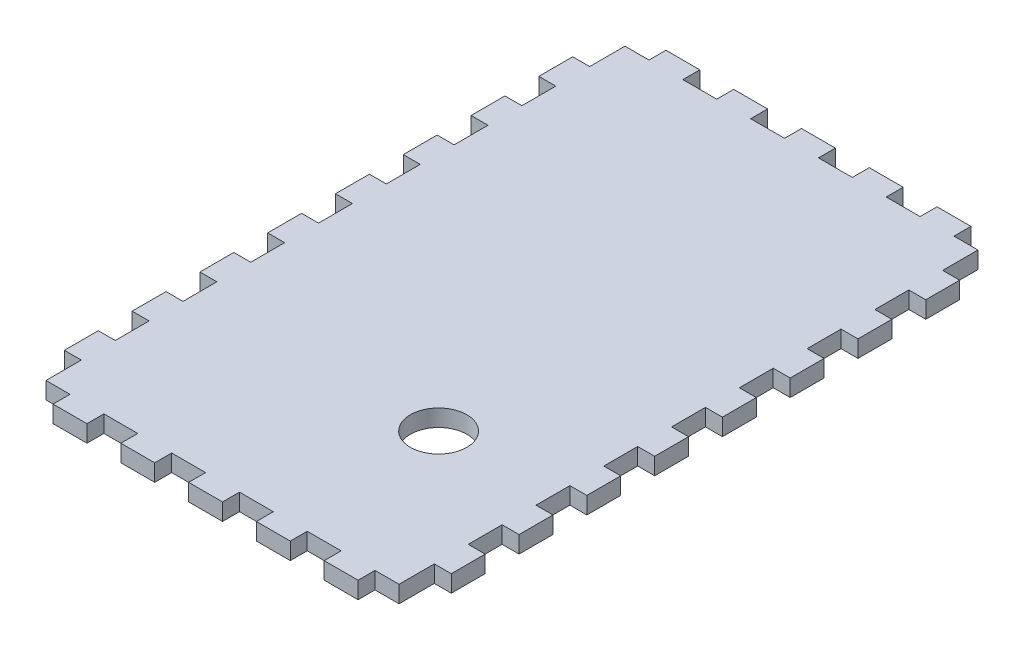
SolidWorks part; units mm, degrees
ref_plane "Front Plane" through (0, 0, 0) normal (0, 0, 1) x (1, 0, 0)
ref_plane "Top Plane" through (0, 0, 0) normal (0, 1, 0) x (1, 0, 0)
ref_plane "Right Plane" through (0, 0, 0) normal (1, 0, 0) x (0, 0, -1)
sketch "Sketch3" plane through (0, 0, 0) normal (0, 1, 0) x (1, 0, 0)
  line L231 (-62.5, -102.5) -> (62.5, -102.5)
  line L232 (-62.5, -102.5) -> (-62.5, 102.5)
  line L233 (-62.5, 102.5) -> (62.5, 102.5)
  line L234 (62.5, -102.5) -> (62.5, 102.5)
  line L235 (-62.5, -102.5) -> (62.5, 102.5) construction
  line L236 (-62.5, 102.5) -> (62.5, -102.5) construction
  point P66 (0, 0)
  dimension "D3" = 205
  dimension "D4" = 125
extrude "Boss-Extrude1" add sketch "Sketch3" along normal blind 6
sketch "Sketch5" plane through (0, 6, 0) normal (0, 1, 0) x (1, 0, 0)
  line L0 (62.5, 102.5) -> (-62.5, 102.5) construction
  line L1 (-54, 102.5) -> (-42, 102.5)
  line L2 (-54, 102.5) -> (-54, 108.5)
  line L3 (-54, 108.5) -> (-42, 108.5)
  line L4 (-42, 102.5) -> (-42, 108.5)
  line L5 (-30, 102.5) -> (-30, 108.5)
  line L6 (-30, 102.5) -> (-18, 102.5)
  line L7 (-18, 102.5) -> (-18, 108.5)
  line L8 (-30, 108.5) -> (-18, 108.5)
  line L9 (-6, 102.5) -> (-6, 108.5)
  line L10 (-6, 102.5) -> (6, 102.5)
  line L11 (6, 102.5) -> (6, 108.5)
  line L12 (-6, 108.5) -> (6, 108.5)
  line L13 (18, 102.5) -> (18, 108.5)
  line L14 (18, 102.5) -> (30, 102.5)
  line L15 (30, 102.5) -> (30, 108.5)
  line L16 (18, 108.5) -> (30, 108.5)
  line L17 (42, 102.5) -> (42, 108.5)
  line L18 (42, 102.5) -> (54, 102.5)
  line L19 (54, 102.5) -> (54, 108.5)
  line L20 (42, 108.5) -> (54, 108.5)
  line L41 (-62.5, 102.5) -> (-62.5, -102.5) construction
  line L43 (62.5, -102.5) -> (62.5, 102.5) construction
  line L44 (-62.5, 90) -> (-68.5, 90)
  line L45 (-62.5, 90) -> (-62.5, 78)
  line L46 (-62.5, 78) -> (-68.5, 78)
  line L47 (-68.5, 90) -> (-68.5, 78)
  line L48 (68.5, 90) -> (68.5, 78)
  line L49 (68.5, 90) -> (62.5, 90)
  line L50 (62.5, 90) -> (62.5, 78)
  line L51 (68.5, 78) -> (62.5, 78)
  line L52 (68.5, 66) -> (68.5, 54)
  line L53 (68.5, 66) -> (62.5, 66)
  line L54 (62.5, 66) -> (62.5, 54)
  line L55 (68.5, 54) -> (62.5, 54)
  line L56 (68.5, 42) -> (68.5, 30)
  line L57 (68.5, 42) -> (62.5, 42)
  line L58 (62.5, 42) -> (62.5, 30)
  line L59 (68.5, 30) -> (62.5, 30)
  line L60 (68.5, 18) -> (68.5, 6)
  line L61 (68.5, 18) -> (62.5, 18)
  line L62 (62.5, 18) -> (62.5, 6)
  line L63 (68.5, 6) -> (62.5, 6)
  line L64 (68.5, -6) -> (68.5, -18)
  line L65 (68.5, -6) -> (62.5, -6)
  line L66 (62.5, -6) -> (62.5, -18)
  line L67 (68.5, -18) -> (62.5, -18)
  line L68 (68.5, -30) -> (68.5, -42)
  line L69 (68.5, -30) -> (62.5, -30)
  line L70 (62.5, -30) -> (62.5, -42)
  line L71 (68.5, -42) -> (62.5, -42)
  line L72 (68.5, -54) -> (68.5, -66)
  line L73 (68.5, -54) -> (62.5, -54)
  line L74 (62.5, -54) -> (62.5, -66)
  line L75 (68.5, -66) -> (62.5, -66)
  line L76 (68.5, -78) -> (68.5, -90)
  line L77 (68.5, -78) -> (62.5, -78)
  line L78 (62.5, -78) -> (62.5, -90)
  line L79 (68.5, -90) -> (62.5, -90)
  line L80 (-62.5, 66) -> (-62.5, 54)
  line L81 (-62.5, 66) -> (-68.5, 66)
  line L82 (-68.5, 66) -> (-68.5, 54)
  line L83 (-62.5, 54) -> (-68.5, 54)
  line L84 (-62.5, 42) -> (-62.5, 30)
  line L85 (-62.5, 42) -> (-68.5, 42)
  line L86 (-68.5, 42) -> (-68.5, 30)
  line L87 (-62.5, 30) -> (-68.5, 30)
  line L88 (-62.5, 18) -> (-62.5, 6)
  line L89 (-62.5, 18) -> (-68.5, 18)
  line L90 (-68.5, 18) -> (-68.5, 6)
  line L91 (-62.5, 6) -> (-68.5, 6)
  line L92 (-62.5, -6) -> (-62.5, -18)
  line L93 (-62.5, -6) -> (-68.5, -6)
  line L94 (-68.5, -6) -> (-68.5, -18)
  line L95 (-62.5, -18) -> (-68.5, -18)
  line L96 (-62.5, -30) -> (-62.5, -42)
  line L97 (-62.5, -30) -> (-68.5, -30)
  line L98 (-68.5, -30) -> (-68.5, -42)
  line L99 (-62.5, -42) -> (-68.5, -42)
  line L100 (-62.5, -54) -> (-62.5, -66)
  line L101 (-62.5, -54) -> (-68.5, -54)
  line L102 (-68.5, -54) -> (-68.5, -66)
  line L103 (-62.5, -66) -> (-68.5, -66)
  line L104 (-62.5, -78) -> (-62.5, -90)
  line L105 (-62.5, -78) -> (-68.5, -78)
  line L106 (-68.5, -78) -> (-68.5, -90)
  line L107 (-62.5, -90) -> (-68.5, -90)
  line L108 (-62.5, 6) -> (-62.5, -6)
  line L109 (-54, -108.5) -> (-54, -102.5)
  line L110 (-54, -108.5) -> (-42, -108.5)
  line L111 (-42, -108.5) -> (-42, -102.5)
  line L112 (-54, -102.5) -> (-42, -102.5)
  line L113 (-30, -108.5) -> (-30, -102.5)
  line L114 (-30, -108.5) -> (-18, -108.5)
  line L115 (-18, -108.5) -> (-18, -102.5)
  line L116 (-30, -102.5) -> (-18, -102.5)
  line L117 (-6, -108.5) -> (-6, -102.5)
  line L118 (-6, -108.5) -> (6, -108.5)
  line L119 (6, -108.5) -> (6, -102.5)
  line L120 (-6, -102.5) -> (6, -102.5)
  line L121 (18, -108.5) -> (18, -102.5)
  line L122 (18, -108.5) -> (30, -108.5)
  line L123 (30, -108.5) -> (30, -102.5)
  line L124 (18, -102.5) -> (30, -102.5)
  line L125 (42, -108.5) -> (42, -102.5)
  line L126 (42, -108.5) -> (54, -108.5)
  line L127 (54, -108.5) -> (54, -102.5)
  line L128 (42, -102.5) -> (54, -102.5)
  point P6 (0, 102.5)
  point P55 (-62.5, 0)
  line M6 (62.5, -102.5) -> (62.5, 102.5)
  line M7 (62.5, 102.5) -> (-62.5, 102.5)
  line M8 (-62.5, 102.5) -> (-62.5, -102.5)
  line M9 (-62.5, -102.5) -> (62.5, -102.5)
  dimension "D1" = 12
  dimension "D2" = 6
  dimension "D5" = 12
  dimension "D6" = 205
  dimension "D8" = 12
  dimension "D9" = 6
  dimension "D12" = 125
  dimension "D13" = 24
  dimension "D3" = 5
  dimension "D4" = 2
  dimension "D10" = 2
  dimension "D11" = 8
extrude "Boss-Extrude2" add sketch "Sketch5" against normal blind 6 contours L122 L123 L121 M9 | L118 L119 L117 M9 | L107 L105 L106 M8 | L103 L101 L102 M8 | L95 L93 L94 M8 | L79 L76 L77 M6 | L71 L68 L69 M6 | L67 L64 L65 M6 | L63 L60 L61 M6 | L59 L56 L57 M6 | L51 L48 L49 M6 | L16 L13 L15 M7 | L12 L9 L11 M7 | L8 L5 L7 M7 | L4 L3 L2 M7 | L87 L85 L86 M8 | L91 L89 L90 M8 | L128 L127 L126 L125 | L116 L115 L114 L113 | L112 L111 L110 L109 | L98 L99 L96 L97 | L74 L75 L72 L73 | L52 L55 L54 L53 | L20 L19 L18 L17 | L45 L46 L47 L44 | L82 L83 L80 L81
sketch "Sketch6" plane through (0, 6, 0) normal (0, 1, 0) x (1, 0, 0)
  line L0 (-6, -108.5) -> (6, -108.5) construction
  line L2 (62.5, -48) -> (32.5, -48)
  line L3 (62.5, -54) -> (62.5, -42) construction
  circle A0 centre (22.5125, -48.5) radius 10
  point P8 (7.6445, -48)
  point P9 (0, 0)
  dimension "D1" = 20
  dimension "D2" = 60
  dimension "D3" = 30
extrude "Cut-Extrude1" cut sketch "Sketch6" against normal blind 6 contours A0
